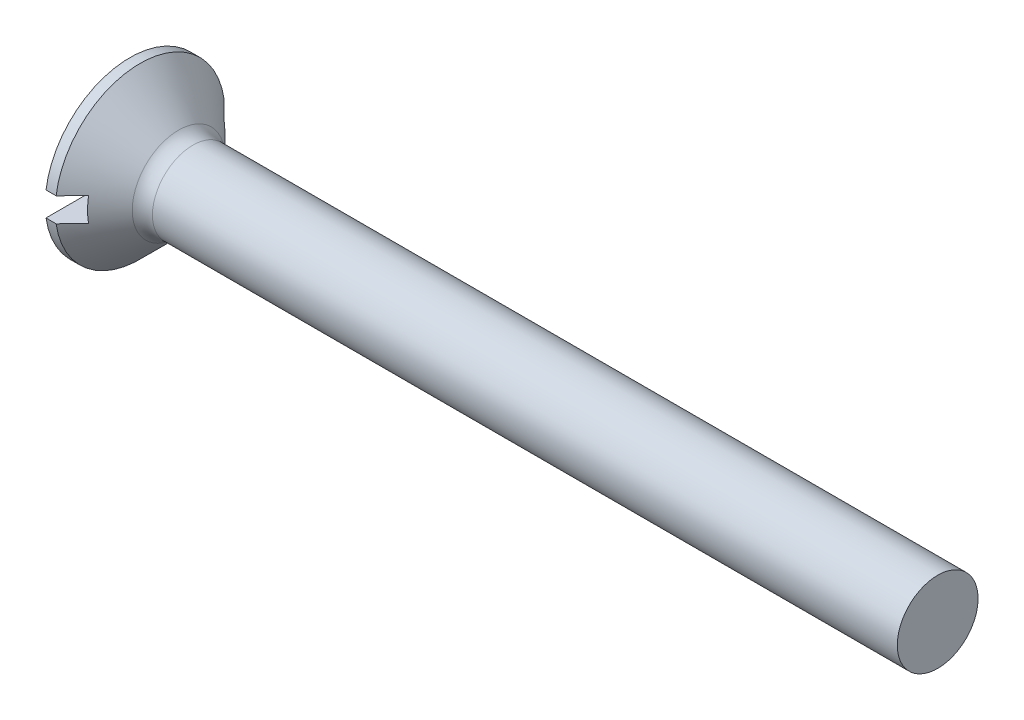
SolidWorks part; units mm, degrees
revolve "Base-Revolve" add sketch "BodySke" angle 360 about L5
sketch "BodySke" plane through (0, 0, 0) normal (0, 0, 1) x (1, 0, 0)
  line L0 (0, 0) -> (0, 4.2)
  line L1 (0, 4.2) -> (0.5, 4.2)
  line L2 (2.7, 2) -> (40, 2)
  line L3 (40, 2) -> (40, 0)
  line L4 (40, 0) -> (0, 0)
  line L5 (-6.35, 0) -> (82.55, 0) construction
  line L6 (2.7, -2) -> (40, -2) construction
  line L7 (0.5, -4.2) -> (2.7, -2) construction
  line L8 (0.5, 4.2) -> (2.7, 2)
  line L9 (0, -4.2) -> (0.5, -4.2) construction
  line L10 (3.4, 3.5875) -> (3.4, -5.9375) construction
  line L11 (0, 6.35) -> (0, -3.175) construction
cosmetic thread "ThreadCosmetic" [suppressed] parameters "Thread_length"=8.6, "Thread_minor"=3.22
extrude "Slot" cut sketch "Sketch2" against normal blind 1.3
sketch "Sketch2" plane through (0, 0, 0) normal (-1, 0, 0) x (0, 0, 1)
  line L0 (-4.2, -0.6) -> (4.2, -0.6)
  line L1 (-4.2, -0.6) -> (-4.2, 0.6)
  line L2 (4.2, 0.6) -> (-4.2, 0.6)
  line L3 (4.2, 0.6) -> (4.2, -0.6)
ref_plane "Plane1" through (0, 0, 0) normal (0, 0, 1) x (1, 0, 0)
ref_plane "Plane2" through (0, 0, 0) normal (0, 1, 0) x (1, 0, 0)
ref_plane "Plane3" through (0, 0, 0) normal (1, 0, 0) x (0, 0, -1)
fillet "Fillet1" radius 1 1 edges at (2.7, 0, 2)
sketch "ThdSchSke" plane through (0, 0, 0) normal (0, 0, 1) x (1, 0, 0)
  line L0 (3.4, -1.61) -> (3.1269, -2)
  line L1 (3.4, -1.61) -> (3.6731, -2)
  line L2 (3.6731, -2) -> (3.6731, -2.5)
  line L3 (-3.175, 0) -> (5.1513, 0) construction
  line L5 (3.6731, -2.5) -> (3.1269, -2.5)
  line L6 (3.1269, -2.5) -> (3.1269, -2)
  line L7 (0, 4.2) -> (0, 0.6) construction
revolve "ThreadSchematic" [suppressed] cut sketch "ThdSchSke" angle 360 about L3
pattern_linear "ThdSchPat" [suppressed]
equation "\"D1@Sketch2\" = \"Slot_width@Sketch2\" / 2"
equation "\"D2@Sketch2\" = \"Head_dia@BodySke\""
equation "\"D3@Sketch2\" = \"D2@Sketch2\" / 2"
equation "\"Thread_length@ThreadCosmetic\" = ((sgn( (\"Length@BodySke\" - \"Advance@BodySke\" * 1.0 - \"Head_ht@BodySke\" ) - \"Thread_nom@BodySke\" )-1)*( (\"Length@BodySke\" - \"Advance@BodySke\" * 1.0 - \"Head_ht@BodySke\" ) - \"Thread_nom@BodySke\" ))/-2+ \"Thread_nom@BodySke\""
equation "\"Thread_minor@ThdSchSke\" = \"Thread_minor@ThreadCosmetic\""
equation "\"Diameter@ThdSchSke\" = \"Diameter@BodySke\""
equation "\"Overcut@ThdSchSke\" = \"Diameter@BodySke\" * 1.25"
equation "\"Start@ThdSchSke\" = 0.000001 + \"Length@BodySke\" - \"Thread_length@ThreadCosmetic\"  '---Countersunk---"
equation "\"Num_threads@ThdSchPat\" = int( \"Thread_length@ThreadCosmetic\" / \"Advance@BodySke\" + 0.999 )  + 1"
equation "\"Advance@ThdSchPat\" = \"Thread_length@ThreadCosmetic\" /  (\"Num_threads@ThdSchPat\" - 1) 'relax it"
